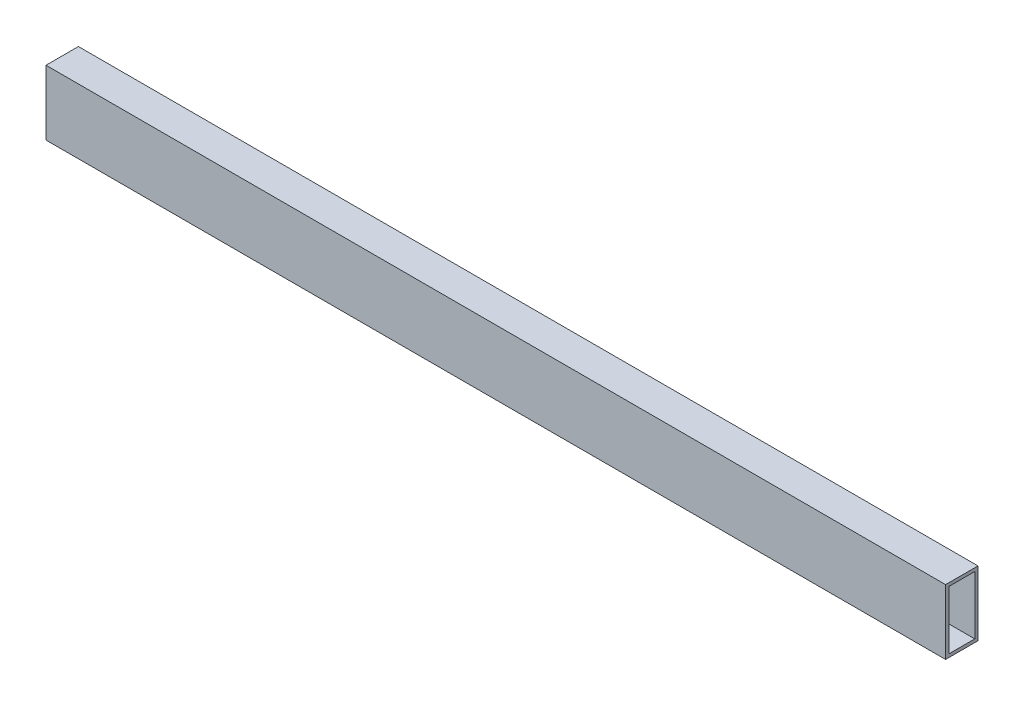
SolidWorks part; units mm, degrees
material "6061-T6 (SS)"
ref_plane "Front" through (0, 0, 0) normal (0, 0, 1) x (1, 0, 0)
ref_plane "Top" through (0, 0, 0) normal (0, 1, 0) x (1, 0, 0)
ref_plane "Right" through (0, 0, 0) normal (1, 0, 0) x (0, 0, -1)
sketch "Sketch1" plane through (0, 0, 0) normal (1, 0, 0) x (0, 0, -1)
  line L1 (-12.7, -25.4) -> (12.7, -25.4)
  line L2 (-12.7, -25.4) -> (-12.7, 25.4)
  line L3 (-12.7, 25.4) -> (12.7, 25.4)
  line L4 (12.7, -25.4) -> (12.7, 25.4)
  line L5 (-12.7, -25.4) -> (12.7, 25.4) construction
  line L6 (-12.7, 25.4) -> (12.7, -25.4) construction
  point P0 (0, 0)
  dimension "D1" = 50.8
  dimension "D2" = 25.4
extrude "Extrude-Thin1" add sketch "Sketch1" along normal blind 704.85 thin thin type one direction reverse wall 2.54
